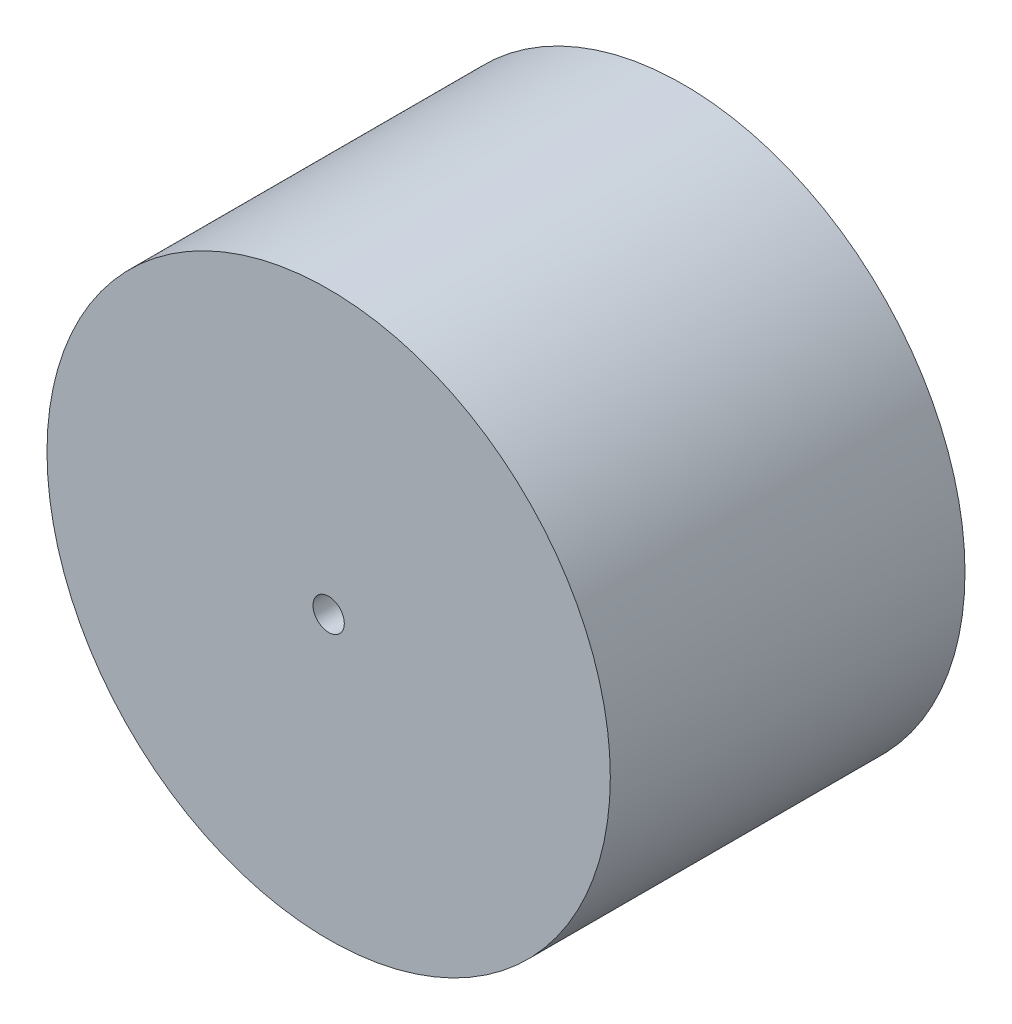
SolidWorks part; units mm, degrees
ref_plane "Alzado" through (0, 0, 0) normal (0, 0, 1) x (1, 0, 0)
ref_plane "Planta" through (0, 0, 0) normal (0, 1, 0) x (1, 0, 0)
ref_plane "Vista lateral" through (0, 0, 0) normal (1, 0, 0) x (0, 0, -1)
sketch "Croquis1" plane through (0, 0, 0) normal (0, 0, 1) x (1, 0, 0)
  circle A0 centre (0, 0) radius 27
  circle A1 centre (0, 0) radius 1.5
  dimension "D1" = 54
extrude "Saliente-Extruir1" add sketch "Croquis1" along normal blind 34
